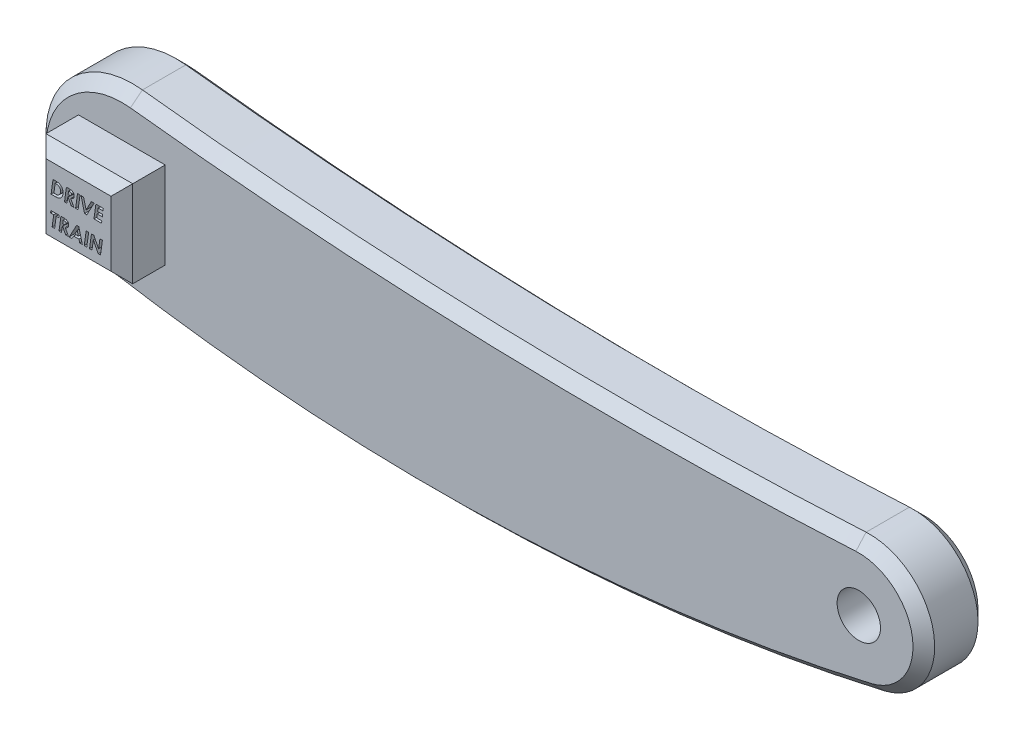
SolidWorks part; units mm, degrees
ref_plane "Front Plane" through (0, 0, 0) normal (0, 0, 1) x (1, 0, 0)
ref_plane "Top Plane" through (0, 0, 0) normal (0, 1, 0) x (1, 0, 0)
ref_plane "Right Plane" through (0, 0, 0) normal (1, 0, 0) x (0, 0, -1)
sketch "Sketch2" plane through (0, 0, 0) normal (0, 0, 1) x (1, 0, 0)
  line L0 (-85, 0) -> (85, 0) construction
  circle A0 centre (-85, 0) radius 20
  circle A1 centre (85, 0) radius 15
  arc A2 (-82.7465, 19.8726) -> (84.1861, 14.9779) centre (29.9265, 1013.5048) ccw
  arc A3 (-88.3618, -19.7154) -> (88.3697, -14.6166) centre (-12.7206, 423.8817) ccw
  point P4 (0, 0)
  dimension "D2" = 40
  dimension "D3" = 30
  dimension "D4" = 450
  dimension "D5" = 1000
  dimension "D1" = 170
extrude "Boss-Extrude1" add sketch "Sketch2" along normal mid plane 15
chamfer "Chamfer1" distance 2.5 angle 45 8 edges at (99.8523, 2.0996, -7.5) (0.6174, 13.9344, -7.5) (-104.8018, 2.8087, -7.5) (0.2568, -25.9311, -7.5) (-104.8018, 2.8087, 7.5) (0.6174, 13.9344, 7.5) (99.8523, 2.0996, 7.5) (0.2568, -25.9311, 7.5)
sketch "Sketch3" plane through (0, 0, 7.5) normal (0, 0, 1) x (1, 0, 0)
  line L1 (-95, 10) -> (-75, 10)
  line L2 (-95, 10) -> (-95, -10)
  line L3 (-95, -10) -> (-75, -10)
  line L4 (-75, 10) -> (-75, -10)
  line L5 (-95, 10) -> (-75, -10) construction
  line L6 (-95, -10) -> (-75, 10) construction
  arc A0 (-82.7465, 19.8726) -> (-88.3618, -19.7154) centre (-85, 0) ccw construction
  point P0 (-85, 0)
  dimension "D1" = 20
  dimension "D2" = 20
  dimension "D3" = 0
extrude "Boss-Extrude2" add sketch "Sketch3" along normal blind 10
sketch "Sketch4" plane through (0, 0, 17.5) normal (0, 0, 1) x (1, 0, 0)
  line L5 (-95, -10) -> (-75, -10) construction
  text T0 "<b><i>DRIVE</i></b>\r\n<b><i>TRAIN</i></b>"
  point P1 (-90.88, 0)
  dimension "D2" = 11
extrude "Cut-Extrude1" cut sketch "Sketch4" against normal blind 2.5
chamfer "Chamfer4" distance 2.5 angle 45 4 edges at (-85, 10, 17.5) (-95, 0, 17.5) (-85, -10, 17.5) (-75, 0, 17.5)
sketch "Sketch5" plane through (0, 0, 7.5) normal (0, 0, 1) x (1, 0, 0)
  circle A0 centre (85, 0) radius 5
extrude "Cut-Extrude2" cut sketch "Sketch5" against normal blind 10
sketch "Sketch6" plane through (0, 0, -7.5) normal (0, 0, -1) x (-1, 0, 0)
  circle A0 centre (85, 0) radius 5
extrude "Boss-Extrude3" add sketch "Sketch6" along normal blind 10
